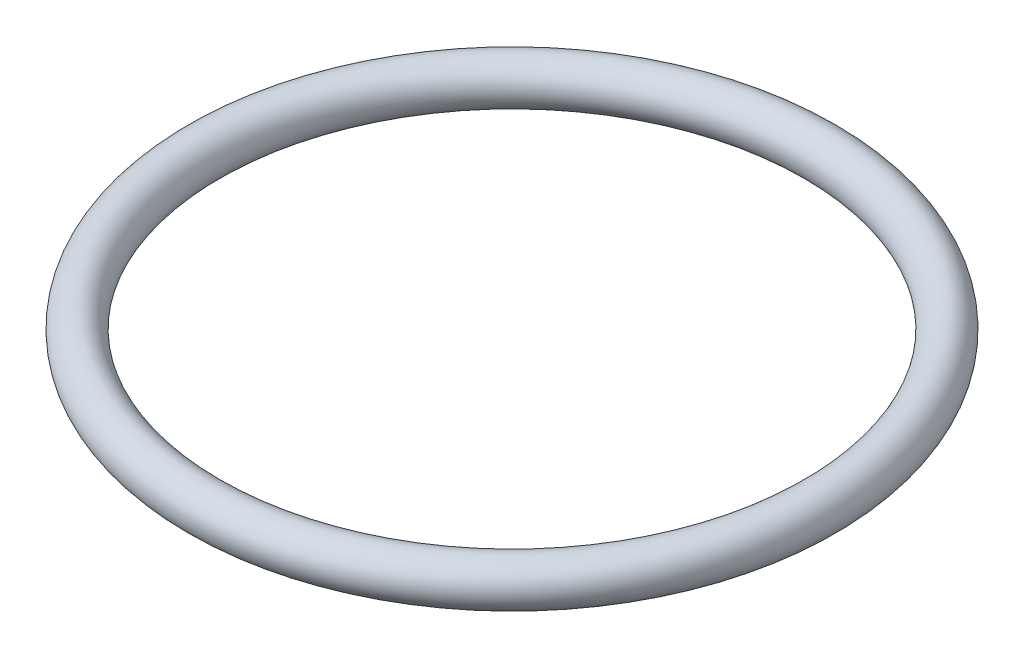
SolidWorks part; units mm, degrees
ref_plane "Front Plane" through (0, 0, 0) normal (0, 0, 1) x (1, 0, 0)
ref_plane "Top Plane" through (0, 0, 0) normal (0, 1, 0) x (1, 0, 0)
ref_plane "Right Plane" through (0, 0, 0) normal (1, 0, 0) x (0, 0, -1)
sketch "Sketch1" plane through (0, 0, 0) normal (0, 0, 1) x (1, 0, 0)
  line L0 (0, 3.1682) -> (0, 0) construction
  line L1 (0, 0) -> (-21, 0) construction
  circle A0 centre (-21, 0) radius 1.5
  dimension "D1" = 3
  dimension "D2" = 21
revolve "Revolve1" add sketch "Sketch1" angle 360 about L0
